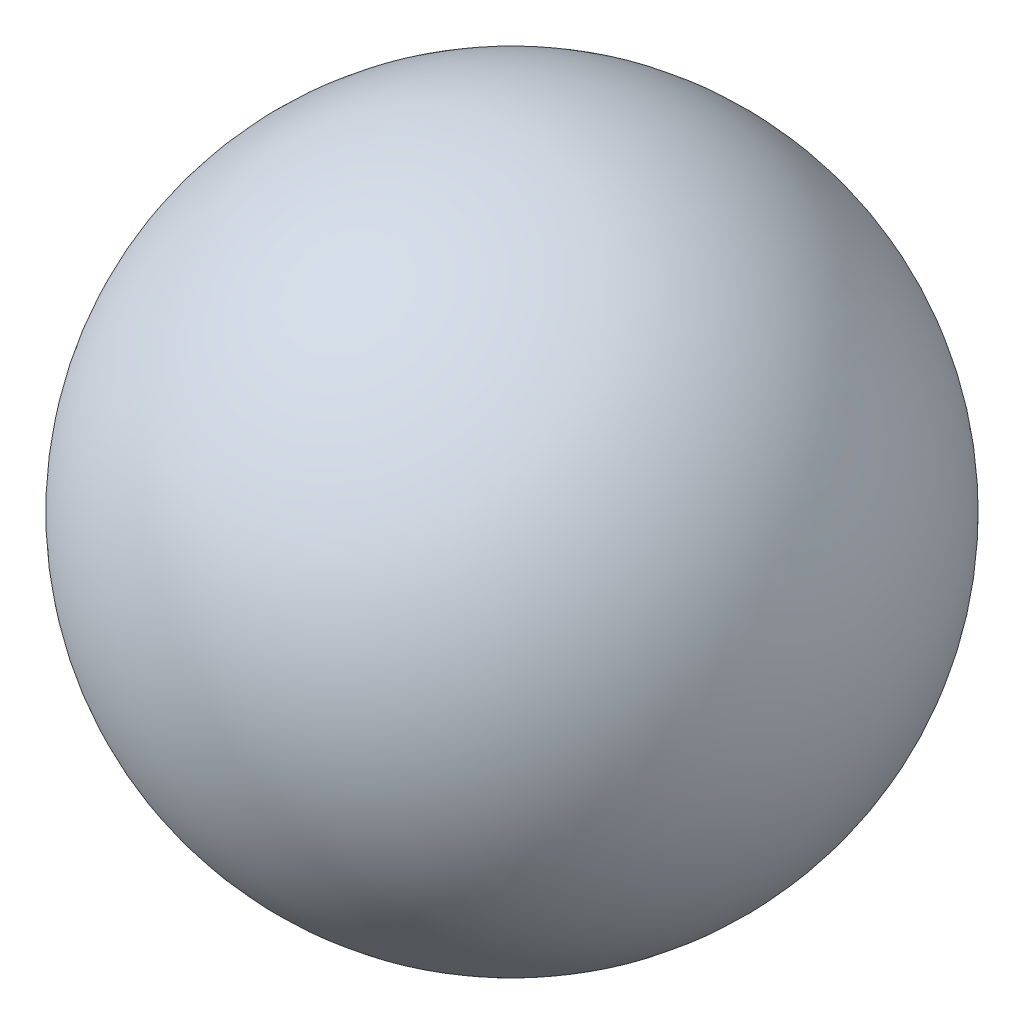
SolidWorks part; units mm, degrees
ref_plane "Front Plane" through (0, 0, 0) normal (0, 0, 1) x (1, 0, 0)
ref_plane "Top Plane" through (0, 0, 0) normal (0, 1, 0) x (1, 0, 0)
ref_plane "Right Plane" through (0, 0, 0) normal (1, 0, 0) x (0, 0, -1)
sketch "Sketch1" plane through (0, 0, 0) normal (0, 0, 1) x (1, 0, 0)
  line L0 (0, -21.5) -> (0, 21.5)
  arc A0 (0, 21.5) -> (0, -21.5) centre (0, 0) cw
  dimension "D1" = 21.5
revolve "Revolve1" add sketch "Sketch1" angle 360 about L0
sketch "Sketch2" plane through (0, 0, 0) normal (0, 0, 1) x (1, 0, 0)
  line L0 (-23.9076, 0) -> (23.9076, 0)
